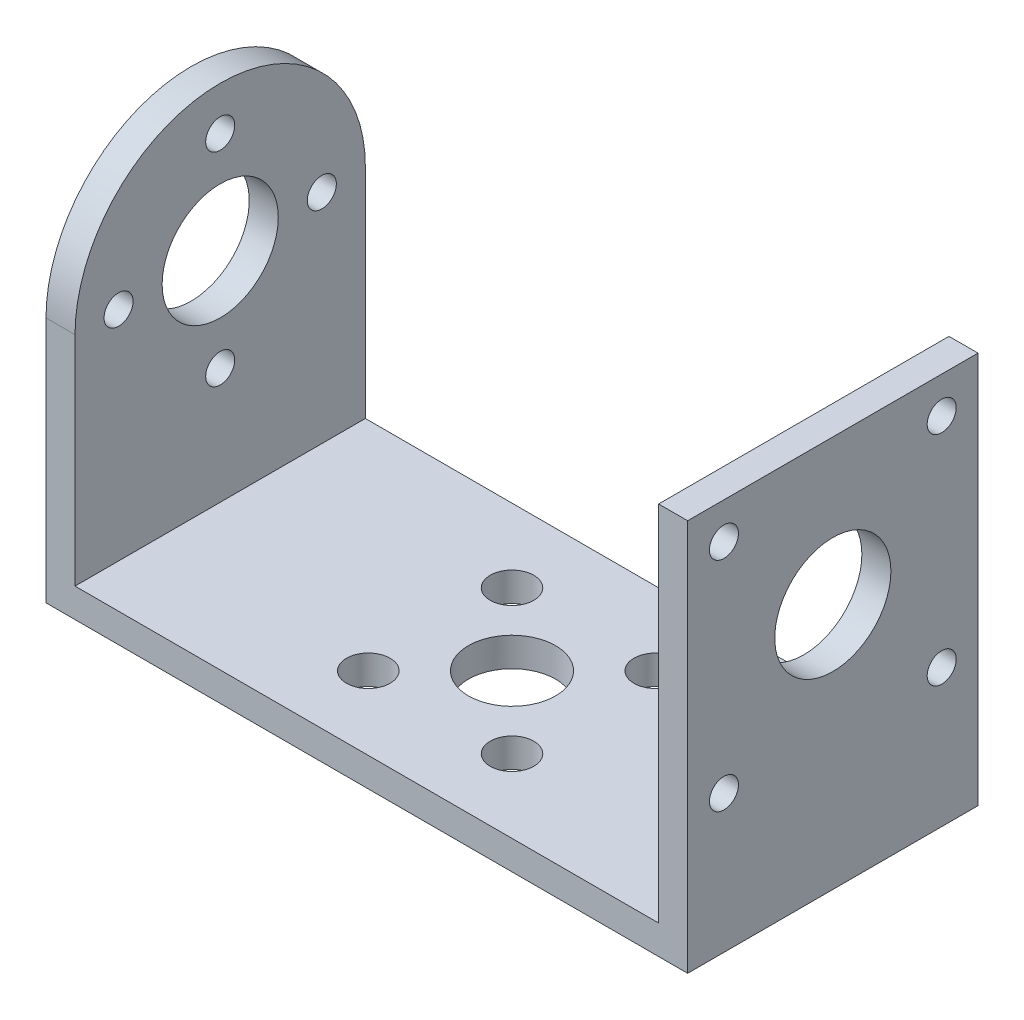
SolidWorks part; units mm, degrees
ref_plane "前视基准面" through (0, 0, 0) normal (0, 0, 1) x (1, 0, 0)
ref_plane "上视基准面" through (0, 0, 0) normal (0, 1, 0) x (1, 0, 0)
ref_plane "右视基准面" through (0, 0, 0) normal (1, 0, 0) x (0, 0, -1)
sketch "草图1" plane through (0, 0, 0) normal (0, 1, 0) x (1, 0, 0)
  line L1 (-22.1, -10) -> (22.1, -10)
  line L2 (-22.1, -10) -> (-22.1, 10)
  line L3 (-22.1, 10) -> (22.1, 10)
  line L4 (22.1, -10) -> (22.1, 10)
  line L5 (-22.1, -10) -> (22.1, 10) construction
  line L6 (-22.1, 10) -> (22.1, -10) construction
  point P0 (0, 0)
  dimension "D1" = 20
  dimension "D2" = 44.2
extrude "凸台-拉伸1" add sketch "草图1" along normal blind 2
sketch "草图2" plane through (0, 2, 0) normal (0, 1, 0) x (1, 0, 0)
  line L0 (0, 10) -> (0, -10) construction
  line L2 (0, 0) -> (7.7612, -7.7612) construction
  line L6 (-7, 0) -> (7, 0) construction
  circle A0 centre (0, 0) radius 3
  circle A1 centre (0, 0) radius 7 construction
  circle A2 centre (4.9497, -4.9497) radius 1.5
  circle A3 centre (-4.9497, -4.9497) radius 1.5
  circle A4 centre (-4.9497, 4.9497) radius 1.5
  circle A5 centre (4.9497, 4.9497) radius 1.5
  arc A7 (-2.9294, -0.6468) -> (-2.9294, 0.6468) centre (-9.8995, 0) ccw construction
  point P20 (0, 0)
extrude "切除-拉伸1" cut sketch "草图2" against normal up to next
sketch "草图3" plane through (-22.1, 0, 0) normal (-1, 0, 0) x (0, 0, 1)
  line L1 (-10, 2) -> (10, 2)
  line L2 (-10, 2) -> (-10, 27)
  line L3 (-10, 27) -> (10, 27)
  line L4 (10, 2) -> (10, 27)
  dimension "D1" = 25
extrude "凸台-拉伸2" add sketch "草图3" against normal blind 2
ref_plane "基准面1" through (0, 0, 0) normal (-1, 0, 0) x (0, 0, 1)
mirror "镜向2" about plane through (0, 0, 0) normal (-1, 0, 0) of "凸台-拉伸2"
sketch "草图4" plane through (-22.1, 0, 0) normal (-1, 0, 0) x (0, 0, 1)
  line L0 (0, 27) -> (0, 0) construction
  line L1 (10, 27) -> (-10, 27) construction
  line L2 (10, 27) -> (10, 0) construction
  line L3 (-10, 27) -> (-10, 0) construction
  line L4 (10, 27) -> (10, 17)
  line L5 (10, 27) -> (-10, 27)
  line L6 (-10, 27) -> (-10, 17)
  arc A0 (10, 17) -> (-10, 17) centre (0, 17) ccw
  circle A1 centre (0, 17) radius 4
  circle A2 centre (0, 24) radius 1
  circle A3 centre (7, 17) radius 1
  circle A4 centre (0, 10) radius 1
  circle A5 centre (-7, 17) radius 1
  point P22 (0, 17)
  line M2 (10, 0) -> (10, 27)
  line M3 (10, 27) -> (-10, 27)
  line M4 (-10, 27) -> (-10, 0)
  dimension "D1" = 10
  dimension "D2" = 7
  dimension "D3" = 4
extrude "切除-拉伸2" cut sketch "草图4" against normal up to next contours A0 L5 M4 | A0 M2 M3 | L0 A4 | A4 L0 | A1 L0 | L0 A1 | A3 | A2 | A5
sketch "草图5" plane through (22.1, 0, 0) normal (1, 0, 0) x (0, 0, -1)
  line L0 (0, 27) -> (0, 0) construction
  line L1 (-10, 27) -> (10, 27) construction
  circle A0 centre (0, 17) radius 4
  circle A1 centre (-7.5, 24.5) radius 1
  circle A2 centre (7.5, 24.5) radius 1
  circle A3 centre (7.5, 9.5) radius 1
  circle A4 centre (-7.5, 9.5) radius 1
  dimension "D1" = 10
  dimension "D2" = 7.5
  dimension "D3" = 7.5
  dimension "D4" = 2
extrude "切除-拉伸3" cut sketch "草图5" against normal up to next
